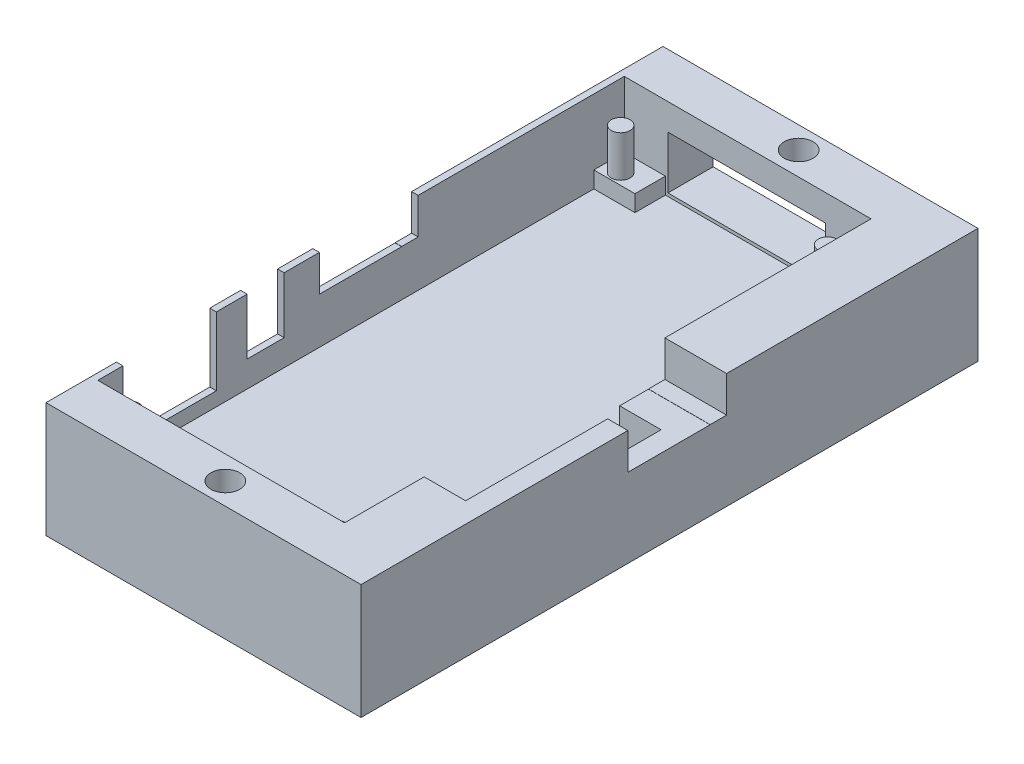
SolidWorks part; units mm, degrees
ref_plane "Alzado" through (0, 0, 0) normal (0, 0, 1) x (1, 0, 0)
ref_plane "Planta" through (0, 0, 0) normal (0, 1, 0) x (1, 0, 0)
ref_plane "Vista lateral" through (0, 0, 0) normal (1, 0, 0) x (0, 0, -1)
sketch "Croquis1" plane through (0, 0, 0) normal (0, 1, 0) x (1, 0, 0)
  line L1 (22.5, 37.5) -> (-22.5, 37.5)
  line L2 (22.5, 37.5) -> (22.5, -37.5)
  line L3 (22.5, -37.5) -> (-22.5, -37.5)
  line L4 (-22.5, 37.5) -> (-22.5, -37.5)
  line L5 (22.5, 37.5) -> (-22.5, -37.5) construction
  line L6 (22.5, -37.5) -> (-22.5, 37.5) construction
  point P0 (0, 0)
  dimension "D1" = 45
  dimension "D2" = 75
extrude "Saliente-Extruir1" add sketch "Croquis1" along normal blind 11
sketch "Croquis2" plane through (0, 11, 0) normal (0, 1, 0) x (1, 0, 0)
  line L1 (15, 32) -> (-15, 32)
  line L2 (15, 32) -> (15, -32)
  line L3 (15, -32) -> (-15, -32)
  line L4 (-15, 32) -> (-15, -32)
  line L5 (15, 32) -> (-15, -32) construction
  line L6 (15, -32) -> (-15, 32) construction
  point P0 (0, 0)
  dimension "D1" = 30
  dimension "D2" = 64
extrude "Cortar-Extruir1" cut sketch "Croquis2" against normal blind 7
sketch "Croquis3" plane through (0, 4, 0) normal (0, 1, 0) x (1, 0, 0)
  line L1 (15, -32) -> (10, -32)
  line L2 (15, -32) -> (15, -28.3)
  line L3 (15, -28.3) -> (10, -28.3)
  line L4 (10, -32) -> (10, -28.3)
  line L9 (-15, -32) -> (-10, -32)
  line L10 (-15, -32) -> (-15, -28.3)
  line L11 (-15, -28.3) -> (-10, -28.3)
  line L12 (-10, -32) -> (-10, -28.3)
  line L14 (15, 32) -> (10, 32)
  line L15 (15, 32) -> (15, 28.3)
  line L16 (15, 28.3) -> (10, 28.3)
  line L17 (10, 32) -> (10, 28.3)
  line L19 (-15, 32) -> (-10, 32)
  line L20 (-15, 32) -> (-15, 28.3)
  line L21 (-15, 28.3) -> (-10, 28.3)
  line L22 (-10, 32) -> (-10, 28.3)
  dimension "D1" = 5
  dimension "D2" = 3.7
  dimension "D3" = 5
  dimension "D4" = 3.7
  dimension "D5" = 3.7
  dimension "D6" = 5
extrude "Saliente-Extruir2" add sketch "Croquis3" along normal blind 2 contours L2 L1 L4 L3 | L10 L9 L12 L11 | L20 L19 L22 L21 | L15 L14 L17 L16
sketch "Croquis4" plane through (0, 6, 0) normal (0, 1, 0) x (1, 0, 0)
  line L0 (-15, -32) -> (-15, -28.3) construction
  line L2 (-15, 32) -> (-15, 28.3) construction
  line L3 (-15, -32) -> (-10, -32) construction
  circle A0 centre (-13.085, -30.04) radius 1.14
  circle A1 centre (12.065, -30.04) radius 1.14
  circle A2 centre (-13.085, 29.65) radius 1.14
  circle A3 centre (12.065, 29.65) radius 1.14
  point P14 (-12.5, -32)
  dimension "D1" = 2.28
  dimension "D3" = 2.28
  dimension "D5" = 2.28
  dimension "D6" = 2.28
  dimension "D2" = 1.915
  dimension "D4" = 25.15
  dimension "D7" = 1.915
  dimension "D8" = 59.69
  dimension "D9" = 25.15
  dimension "D10" = 59.69
  dimension "D11" = 1.96
extrude "Saliente-Extruir3" add sketch "Croquis4" along normal blind 5
sketch "Croquis8" plane through (0, 11, 0) normal (0, 1, 0) x (1, 0, 0)
  line L0 (15, -32) -> (15, 32) construction
  line L1 (15, -22.3226) -> (20.0427, -22.3226)
  line L2 (15, -22.3226) -> (15, 1.435)
  line L3 (15, 1.435) -> (20.0427, 1.435)
  line L4 (20.0427, -22.3226) -> (20.0427, 1.435)
extrude "Cortar-Extruir2" cut sketch "Croquis8" against normal blind 12
sketch "Croquis10" plane through (0, 11, 0) normal (0, 1, 0) x (1, 0, 0)
  line L0 (-22.5, -37.5) -> (22.5, -37.5) construction
  line L1 (-22.5, 37.5) -> (-15.7956, 37.5)
  line L2 (-22.5, 37.5) -> (-22.5, -37.5)
  line L3 (-22.5, -37.5) -> (-15.7956, -37.5)
  line L4 (-15.7956, 37.5) -> (-15.7956, -37.5)
  dimension "D1" = 6.7044
extrude "Cortar-Extruir3" cut sketch "Croquis10" against normal blind 18 contours L2 L1 L4 L3
sketch "Croquis11" plane through (-15.7956, 0, 0) normal (-1, 0, 0) x (0, 0, 1)
  line L0 (-37.5, 11) -> (37.5, 11) construction
  line L1 (28.9484, 11) -> (17.5889, 11)
  line L2 (28.9484, 11) -> (28.9484, 5.6897)
  line L3 (28.9484, 5.6897) -> (17.5889, 5.6897)
  line L4 (17.5889, 11) -> (17.5889, 5.6897)
  line L5 (30.7476, 11) -> (30.7476, 0)
  line L6 (13.8476, 11) -> (9.3476, 11)
  line L7 (13.8476, 11) -> (13.8476, 7.1634)
  line L8 (13.8476, 7.1634) -> (9.3476, 7.1634)
  line L9 (9.3476, 11) -> (9.3476, 7.1634)
  line L10 (-37.5, 0) -> (37.5, 0) construction
  line M9 (37.5, 11) -> (-37.5, 11)
  dimension "D1" = 16.9
  dimension "D3" = 4.5
extrude "Cortar-Extruir4" cut sketch "Croquis11" against normal blind 1 contours L4 L3 L2 M9 | L9 L8 L7 M9
sketch "Croquis13" plane through (-15.7956, 0, 0) normal (-1, 0, 0) x (0, 0, 1)
  line L0 (-37.5, 11) -> (9.3476, 11) construction
  line L1 (-4.9385, 11) -> (5.0615, 11)
  line L2 (-4.9385, 11) -> (-4.9385, 9.6013)
  line L3 (-4.9385, 9.6013) -> (5.0615, 9.6013)
  line L4 (5.0615, 11) -> (5.0615, 9.6013)
  line L6 (-6.9385, 11) -> (-3.2085, 11)
  line L7 (30.0615, 11) -> (30.0615, 0)
  line L8 (28.9484, 11) -> (37.5, 11) construction
  line L9 (-37.5, 0) -> (37.5, 0) construction
  line L10 (-6.9385, 11) -> (-6.9385, 9.6225)
  line L11 (-6.9385, 9.6225) -> (-3.2085, 9.6225)
  line L12 (-3.2085, 11) -> (-3.2085, 9.6225)
  point P16 (30.0615, 5.5)
  dimension "D1" = 25
  dimension "D2" = 10
  dimension "D3" = 33.27
  dimension "D4" = 37
  dimension "D5" = 1.3775
extrude "Cortar-Extruir5" cut sketch "Croquis13" against normal blind 38.3 contours L1 L4 L3 L2 | L10 L6 L12 L11
sketch "Croquis14" plane through (0, 11, 0) normal (0, 1, 0) x (1, 0, 0)
  line L0 (-15.7956, -37.5) -> (22.5, -37.5) construction
  line L1 (22.5, 37.5) -> (-15.7956, 37.5) construction
  circle A0 centre (3.3522, -34.85) radius 1.75
  circle A1 centre (3.3522, 34.85) radius 1.75
  dimension "D1" = 3.5
  dimension "D2" = 3.5
  dimension "D3" = 2.65
  dimension "D4" = 2.65
sketch "Croquis15" plane through (0, 0, 0) normal (0, -1, 0) x (1, 0, 0)
  line L0 (22.5, -37.5) -> (-15.7956, -37.5) construction
  line L1 (-15.7956, 37.5) -> (22.5, 37.5) construction
  circle A0 centre (3.3522, -34.85) radius 1.75
  circle A1 centre (3.3522, 34.85) radius 1.75
  dimension "D1" = 3.5
  dimension "D2" = 3.5
  dimension "D3" = 2.65
  dimension "D4" = 2.65
extrude "Cortar-Extruir7" cut sketch "Croquis15" against normal blind 3
sketch "Croquis16" plane through (0, 0, -37.5) normal (0, 0, -1) x (-1, 0, 0)
  line L1 (9.6962, 4.3794) -> (-9.4509, 4.3794)
  line L2 (9.6962, 4.3794) -> (9.6962, 10.7846)
  line L3 (9.6962, 10.7846) -> (-9.4509, 10.7846)
  line L4 (-9.4509, 4.3794) -> (-9.4509, 10.7846)
extrude "Cortar-Extruir8" cut sketch "Croquis16" against normal blind 10
sketch "Croquis17" plane through (0, 11, 0) normal (0, 1, 0) x (1, 0, 0)
  line L0 (22.5, 6.9385) -> (22.5, 37.5) construction
  line L1 (-15.7956, 6.9385) -> (-15, 6.9385)
  line L2 (-15.7956, 6.9385) -> (-15.7956, 32)
  line L3 (-15.7956, 32) -> (-15, 32)
  line L4 (-15, 6.9385) -> (-15, 32)
  line L5 (-15.7956, 37.5) -> (22.5, 37.5)
  line L6 (-15.7956, 37.5) -> (-15.7956, 32)
  line L7 (-15.7956, 32) -> (22.5, 32)
  line L8 (22.5, 37.5) -> (22.5, 32)
  line L9 (-15.7956, -37.5) -> (22.5, -37.5) construction
  line L10 (15, 32) -> (22.5, 32)
  line L11 (15, 32) -> (15, 6.9385)
  line L12 (15, 6.9385) -> (22.5, 6.9385)
  line L13 (22.5, 32) -> (22.5, 6.9385)
  line L14 (-15.7956, -5.0615) -> (-15, -5.0615)
  line L15 (-15.7956, -5.0615) -> (-15.7956, -9.3476)
  line L16 (-15.7956, -9.3476) -> (-15, -9.3476)
  line L17 (-15, -5.0615) -> (-15, -9.3476)
  line L18 (-15.7956, -13.8476) -> (-15, -13.8476)
  line L19 (-15.7956, -13.8476) -> (-15.7956, -17.5889)
  line L20 (-15.7956, -17.5889) -> (-15, -17.5889)
  line L21 (-15, -13.8476) -> (-15, -17.5889)
  line L22 (20.0427, -5.0615) -> (22.5, -5.0615)
  line L23 (20.0427, -5.0615) -> (20.0427, -37.5)
  line L24 (20.0427, -37.5) -> (22.5, -37.5)
  line L25 (22.5, -5.0615) -> (22.5, -37.5)
  line L26 (15, -22.3226) -> (20.0427, -22.3226)
  line L27 (15, -22.3226) -> (15, -37.5)
  line L28 (15, -37.5) -> (20.0427, -37.5)
  line L29 (20.0427, -22.3226) -> (20.0427, -37.5)
  line L30 (-15.7956, -28.9484) -> (-15, -28.9484)
  line L31 (-15.7956, -28.9484) -> (-15.7956, -37.5)
  line L32 (-15.7956, -37.5) -> (-15, -37.5)
  line L33 (-15, -28.9484) -> (-15, -37.5)
  line L35 (-15, -32) -> (15, -32)
  line L36 (-15, -32) -> (-15, -37.5)
  line L37 (-15, -37.5) -> (15, -37.5)
  line L38 (15, -32) -> (15, -37.5)
extrude "Saliente-Extruir4" add sketch "Croquis17" along normal blind 3
sketch "Croquis18" plane through (0, 14, 0) normal (0, 1, 0) x (1, 0, 0)
  circle A0 centre (3.3522, -34.85) radius 1.75
  circle A1 centre (3.3522, 34.85) radius 1.75
extrude "Cortar-Extruir9" cut sketch "Croquis18" against normal blind 3
